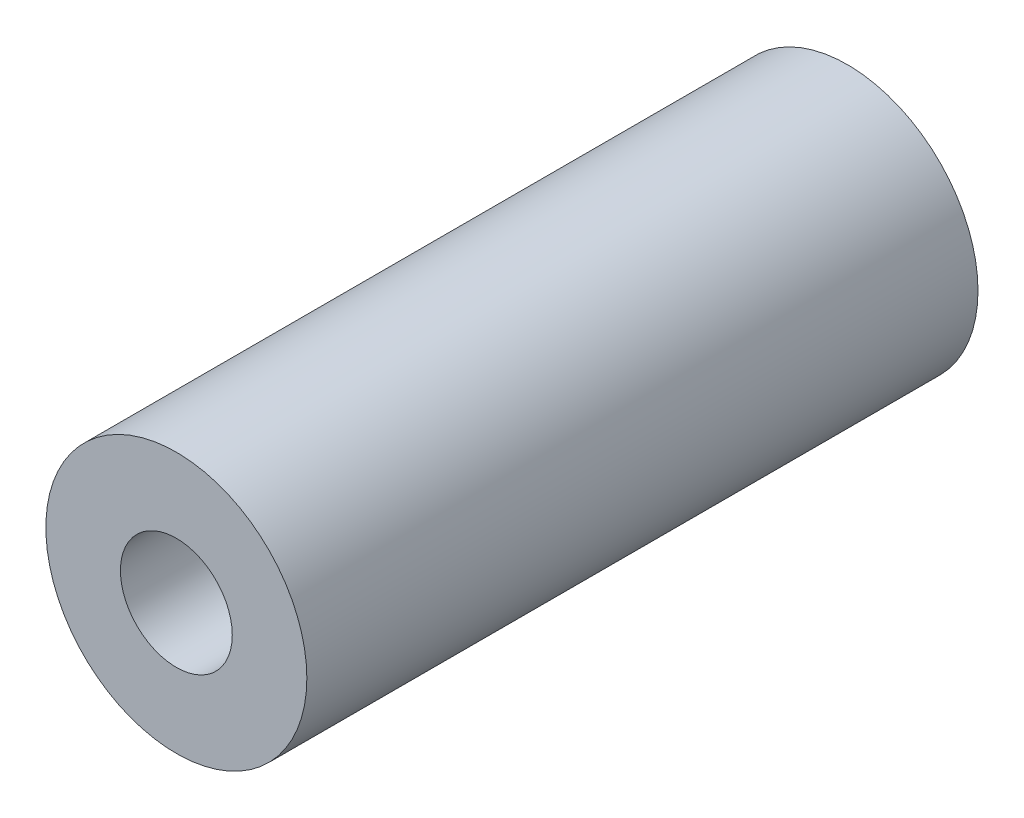
SolidWorks part; units mm, degrees
material "6061-T6 (SS)"
ref_plane "Front Plane" through (0, 0, 0) normal (0, 0, 1) x (1, 0, 0)
ref_plane "Top Plane" through (0, 0, 0) normal (0, 1, 0) x (1, 0, 0)
ref_plane "Right Plane" through (0, 0, 0) normal (1, 0, 0) x (0, 0, -1)
sketch "Sketch1" plane through (0, 0, 0) normal (0, 0, 1) x (1, 0, 0)
  circle A0 centre (0, 0) radius 11.1125
  circle A1 centre (0, 0) radius 4.7625
  dimension "D1" = 22.225
  dimension "D2" = 9.525
extrude "Boss-Extrude1" add sketch "Sketch1" along normal blind 57.15
